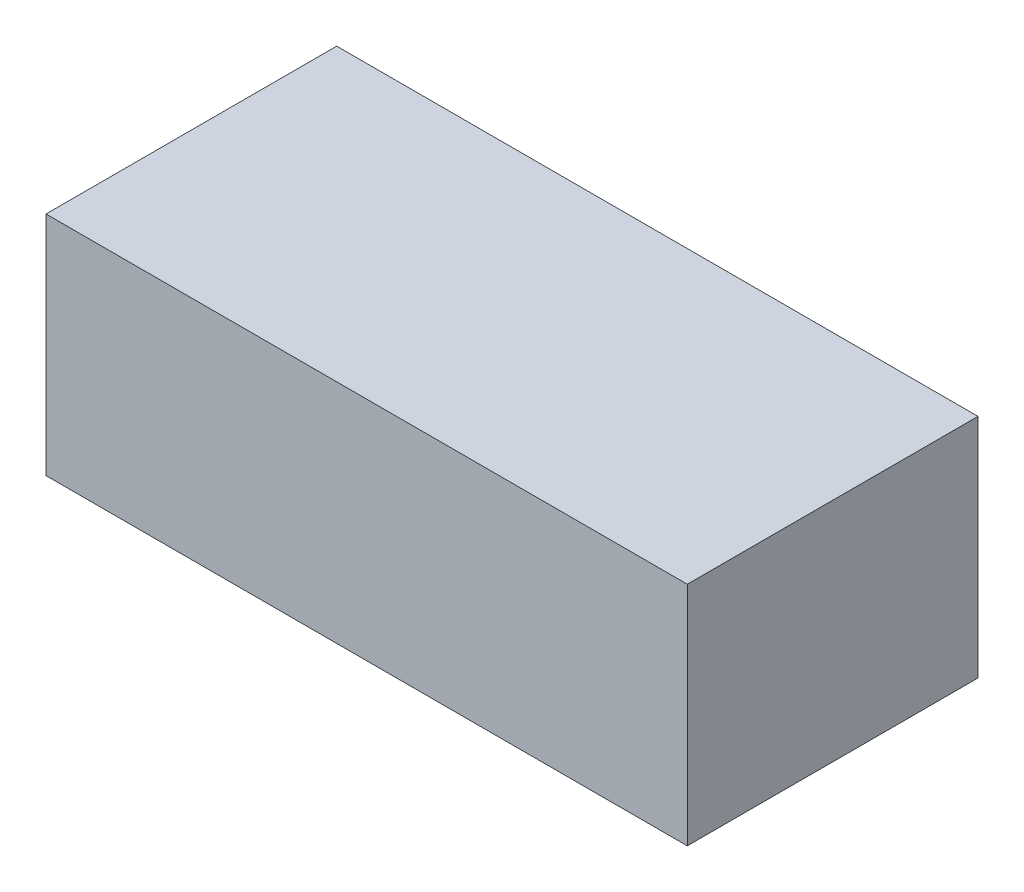
SolidWorks part; units mm, degrees
material "ABS"
ref_plane "Front" through (0, 0, 0) normal (0, 0, 1) x (1, 0, 0)
ref_plane "Top" through (0, 0, 0) normal (0, 1, 0) x (1, 0, 0)
ref_plane "Right" through (0, 0, 0) normal (1, 0, 0) x (0, 0, -1)
sketch "Sketch2" plane through (0, 0, 0) normal (0, 1, 0) x (1, 0, 0)
  line L1 (-37.5, -17) -> (37.5, -17)
  line L2 (-37.5, -17) -> (-37.5, 17)
  line L3 (-37.5, 17) -> (37.5, 17)
  line L4 (37.5, -17) -> (37.5, 17)
  line L5 (-37.5, -17) -> (37.5, 17) construction
  line L6 (-37.5, 17) -> (37.5, -17) construction
  point P0 (0, 0)
  dimension "D1" = 75
  dimension "D2" = 34
extrude "Boss-Extrude1" add sketch "Sketch2" along normal blind 26.5
